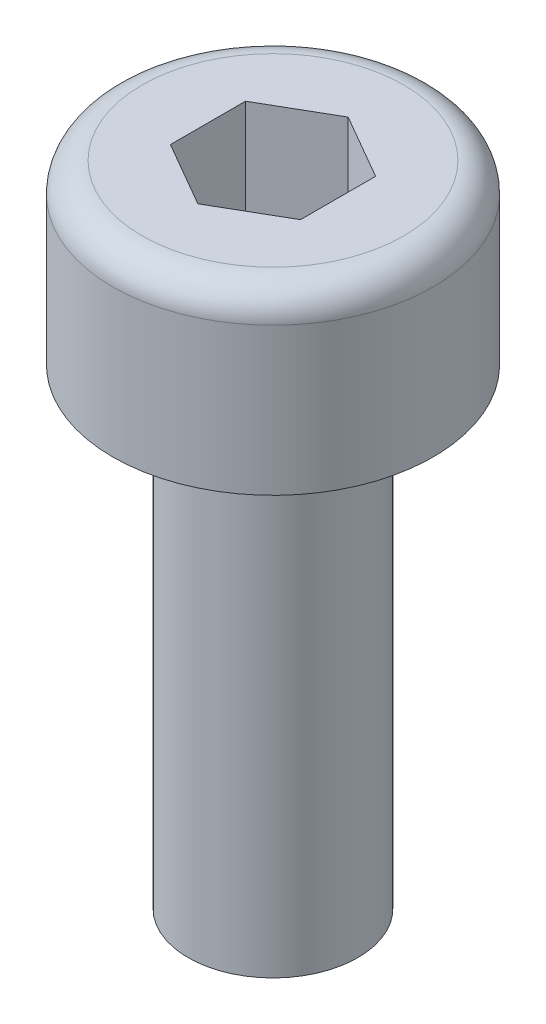
SolidWorks part; units mm, degrees
ref_plane "Front Plane" through (0, 0, 0) normal (0, 0, 1) x (1, 0, 0)
ref_plane "Top Plane" through (0, 0, 0) normal (0, 1, 0) x (1, 0, 0)
ref_plane "Right Plane" through (0, 0, 0) normal (1, 0, 0) x (0, 0, -1)
sketch "Sketch1" plane through (0, 0, 0) normal (0, 1, 0) x (1, 0, 0)
  circle A0 centre (0, 0) radius 2.72
  dimension "D1" = 5.44
extrude "Boss-Extrude1" add sketch "Sketch1" along normal blind 3
sketch "Sketch2" plane through (0, 0, 0) normal (0, -1, 0) x (1, 0, 0)
  circle A0 centre (0, 0) radius 1.44
  dimension "D1" = 2.88
extrude "Boss-Extrude2" add sketch "Sketch2" along normal blind 8
sketch "Sketch3" plane through (0, 3, 0) normal (0, 1, 0) x (1, 0, 0)
  line L1 (1.1042, 0.6375) -> (0, 1.275)
  line L2 (0, 1.275) -> (-1.1042, 0.6375)
  line L3 (-1.1042, 0.6375) -> (-1.1042, -0.6375)
  line L4 (-1.1042, -0.6375) -> (0, -1.275)
  line L5 (0, -1.275) -> (1.1042, -0.6375)
  line L6 (1.1042, -0.6375) -> (1.1042, 0.6375)
  circle A0 centre (0, 0) radius 1.1042 construction
  dimension "D1" = 2.55
extrude "Cut-Extrude1" cut sketch "Sketch3" against normal blind 1.95
fillet "Fillet1" radius 0.5 1 edges at (0, 3, 2.72)
